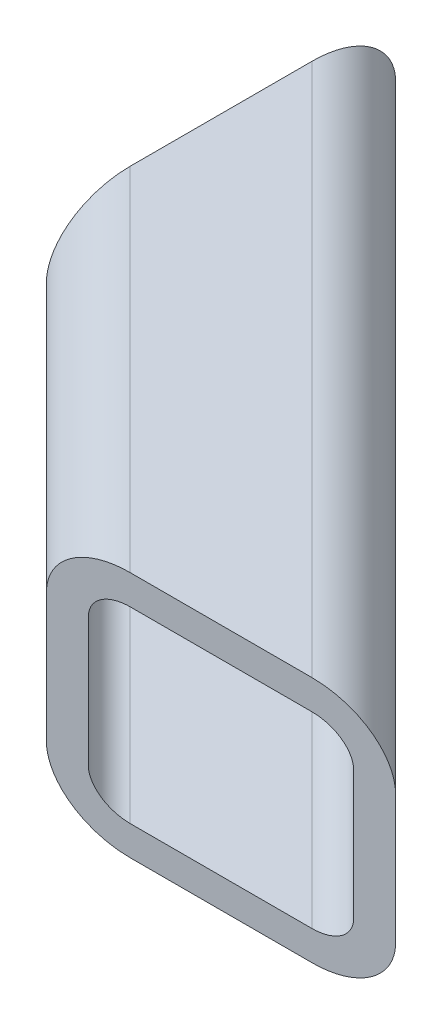
SolidWorks part; units mm, degrees
material "AISI 1020"
ref_plane "Front Plane" through (0, 0, 0) normal (0, 0, 1) x (1, 0, 0)
ref_plane "Top Plane" through (0, 0, 0) normal (0, 1, 0) x (1, 0, 0)
ref_plane "Right Plane" through (0, 0, 0) normal (1, 0, 0) x (0, 0, -1)
sketch3d "3DSketch1"
  line L0 (0, 0, 0) -> (63.5, 0, 63.5)
  line L1 (0, 0, 0) -> (4.9227, 0, 0) construction
  line L2 (0, 0, 0) -> (0, 0, 63.5) construction
  line L3 (0, 0, 63.5) -> (63.5, 0, 63.5) construction
  dimension "D1" = 45
  dimension "D2" = 90
  dimension "D3" = 63.5
other "Sq_rect_tubing_weldment_profiles SQ TUBE 1 X 1 X .120 WALL(1)"
ref_plane "Plane1" through (0, 0, 0) normal (0.7071, 0, 0.7071) x (0.7071, 0, -0.7071)
sketch "Sketch121" plane through (0, 0, 0) normal (0.7071, 0, 0.7071) x (0.7071, 0, -0.7071)
  line L0 (-6.604, -9.652) -> (6.604, -9.652)
  line L1 (-9.652, -6.604) -> (-9.652, 6.604)
  line L2 (6.604, 9.652) -> (-6.604, 9.652)
  line L3 (9.652, 6.604) -> (9.652, -6.604)
  line L4 (-6.604, -12.7) -> (6.604, -12.7)
  line L5 (-12.7, -6.604) -> (-12.7, 6.604)
  line L6 (6.604, 12.7) -> (-6.604, 12.7)
  line L7 (12.7, 6.604) -> (12.7, -6.604)
  line L8 (-12.7, 0) -> (-9.652, 0) construction
  line L9 (-9.652, 0) -> (9.652, 0) construction
  line L10 (9.652, 0) -> (12.7, 0) construction
  line L11 (0, 12.7) -> (0, 9.652) construction
  line L12 (0, 9.652) -> (0, -9.652) construction
  line L13 (0, -9.652) -> (0, -12.7) construction
  arc A0 (12.7, 6.604) -> (6.604, 12.7) centre (6.604, 6.604) ccw
  arc A1 (6.604, -12.7) -> (12.7, -6.604) centre (6.604, -6.604) ccw
  arc A2 (-12.7, -6.604) -> (-6.604, -12.7) centre (-6.604, -6.604) ccw
  arc A3 (-6.604, 12.7) -> (-12.7, 6.604) centre (-6.604, 6.604) ccw
  arc A4 (-6.604, 9.652) -> (-9.652, 6.604) centre (-6.604, 6.604) ccw
  arc A5 (9.652, 6.604) -> (6.604, 9.652) centre (6.604, 6.604) ccw
  arc A6 (6.604, -9.652) -> (9.652, -6.604) centre (6.604, -6.604) ccw
  arc A7 (-9.652, -6.604) -> (-6.604, -9.652) centre (-6.604, -6.604) ccw
  point P6 (-12.7, -12.7)
  point P33 (-12.7, 12.7)
  point P34 (12.7, 12.7)
  point P35 (12.7, 12.7)
  point P36 (12.7, -12.7)
  point P37 (0, 0)
  point P38 (12.7, -12.7)
  point P39 (-12.7, -12.7)
  point P40 (-12.7, 12.7)
  point P41 (-19.05, 0)
  point P42 (0, 19.05)
  point P43 (0, -19.05)
  point P44 (19.05, 0)
  point P45 (0, 0)
  dimension "D1" = 3.048
  dimension "D2" = 6.35
  dimension "D3" = 6.35
  dimension "D4" = 6.35
  dimension "D5" = 6.35
sketch "Sketch122" plane through (0, 12.7, 0) normal (0, 1, 0) x (1, 0, 0)
  line L0 (8.9803, 8.9803) -> (8.9803, -26.9408)
  line L1 (54.5197, -72.4803) -> (-8.9803, -8.9803) construction
  line L2 (72.4803, -54.5197) -> (36.5592, -54.5197)
  line L3 (8.9803, 8.9803) -> (-8.9803, -8.9803)
  line L4 (-8.9803, -8.9803) -> (8.9803, -26.9408)
  line L5 (36.5592, -54.5197) -> (54.5197, -72.4803)
  line L6 (54.5197, -72.4803) -> (72.4803, -54.5197)
extrude "Cut-Extrude1" cut sketch "Sketch122" against normal up to surface (25.4 mm away) up to face at (31.75, -12.7, 31.75)
equation "\"D1@Sketch121\"= \"Thickness@Sketch121\""
